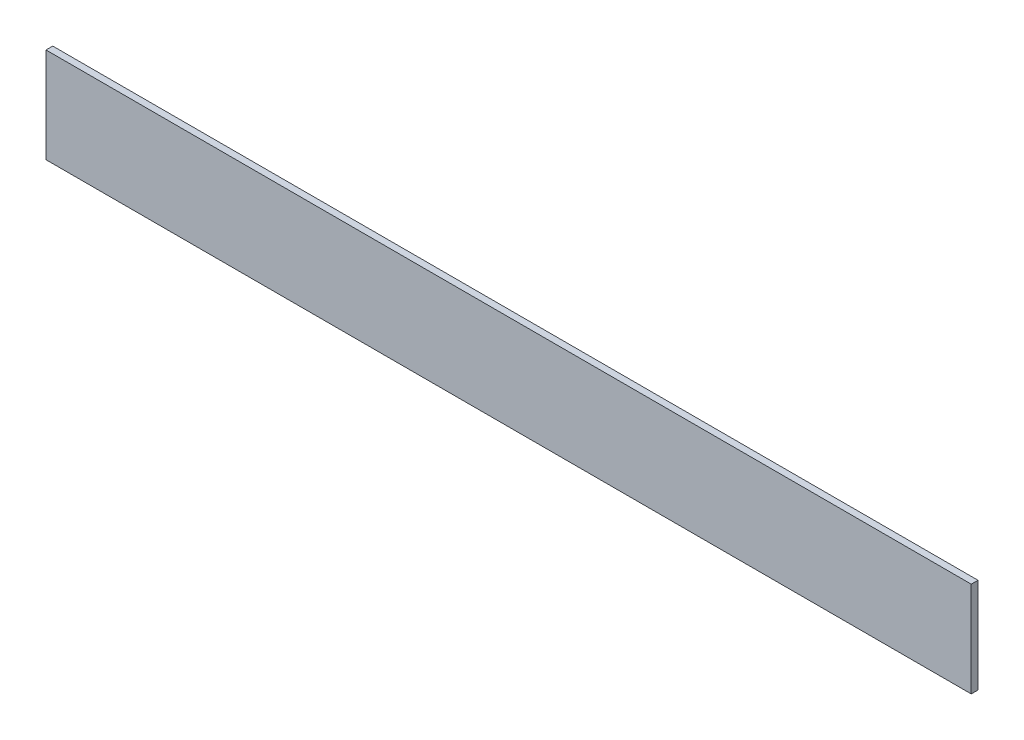
SolidWorks part; units mm, degrees
ref_plane "Front Plane" through (0, 0, 0) normal (0, 0, 1) x (1, 0, 0)
ref_plane "Top Plane" through (0, 0, 0) normal (0, 1, 0) x (1, 0, 0)
ref_plane "Right Plane" through (0, 0, 0) normal (1, 0, 0) x (0, 0, -1)
sketch "Sketch1" plane through (0, 0, 0) normal (0, 0, 1) x (1, 0, 0)
  line L1 (-217.4875, -22.352) -> (217.4875, -22.352)
  line L2 (-217.4875, -22.352) -> (-217.4875, 22.352)
  line L3 (-217.4875, 22.352) -> (217.4875, 22.352)
  line L4 (217.4875, -22.352) -> (217.4875, 22.352)
  line L5 (-217.4875, -22.352) -> (217.4875, 22.352) construction
  line L6 (-217.4875, 22.352) -> (217.4875, -22.352) construction
  point P0 (0, 0)
  dimension "D1" = 44.704
  dimension "D2" = 434.975
extrude "Boss-Extrude1" add sketch "Sketch1" along normal blind 3.175
sketch "Sketch5" plane through (0, 0, 3.175) normal (0, 0, 1) x (1, 0, 0)
  line L8 (217.4875, 38.608) -> (217.4875, 68.072)
  line L9 (-204.7875, 25.908) -> (204.7875, 25.908)
  line L10 (-217.4875, 68.072) -> (-217.4875, 38.608)
  line L11 (214.9475, 70.612) -> (-214.9475, 70.612)
  line L12 (217.4875, 86.868) -> (217.4875, 116.332)
  line L13 (-204.7875, 74.168) -> (204.7875, 74.168)
  line L14 (-217.4875, 116.332) -> (-217.4875, 86.868)
  line L15 (214.9475, 118.872) -> (-214.9475, 118.872)
  line L16 (217.4875, 135.128) -> (217.4875, 164.592)
  line L17 (-204.7875, 122.428) -> (204.7875, 122.428)
  line L18 (-217.4875, 164.592) -> (-217.4875, 135.128)
  line L19 (214.9475, 167.132) -> (-214.9475, 167.132)
  line L20 (217.4875, 183.388) -> (217.4875, 212.852)
  line L21 (-204.7875, 170.688) -> (204.7875, 170.688)
  line L22 (-217.4875, 212.852) -> (-217.4875, 183.388)
  line L23 (214.9475, 215.392) -> (-214.9475, 215.392)
  line L24 (217.4875, 231.648) -> (217.4875, 261.112)
  line L25 (-204.7875, 218.948) -> (204.7875, 218.948)
  line L26 (-217.4875, 261.112) -> (-217.4875, 231.648)
  line L27 (214.9475, 263.652) -> (-214.9475, 263.652)
  line L28 (217.4875, 279.908) -> (217.4875, 309.372)
  line L29 (-204.7875, 267.208) -> (204.7875, 267.208)
  line L30 (-217.4875, 309.372) -> (-217.4875, 279.908)
  line L31 (214.9475, 311.912) -> (-214.9475, 311.912)
  circle A12 centre (166.6875, 60.96) radius 2.8956
  arc A13 (217.4875, 68.072) -> (214.9475, 70.612) centre (214.9475, 68.072) ccw
  arc A14 (204.7875, 25.908) -> (217.4875, 38.608) centre (204.7875, 38.608) ccw
  circle A15 centre (-166.6875, 60.96) radius 2.8956
  arc A16 (-217.4875, 38.608) -> (-204.7875, 25.908) centre (-204.7875, 38.608) ccw
  arc A17 (-214.9475, 70.612) -> (-217.4875, 68.072) centre (-214.9475, 68.072) ccw
  circle A18 centre (166.6875, 109.22) radius 2.8956
  arc A19 (217.4875, 116.332) -> (214.9475, 118.872) centre (214.9475, 116.332) ccw
  arc A20 (204.7875, 74.168) -> (217.4875, 86.868) centre (204.7875, 86.868) ccw
  circle A21 centre (-166.6875, 109.22) radius 2.8956
  arc A22 (-217.4875, 86.868) -> (-204.7875, 74.168) centre (-204.7875, 86.868) ccw
  arc A23 (-214.9475, 118.872) -> (-217.4875, 116.332) centre (-214.9475, 116.332) ccw
  circle A24 centre (166.6875, 157.48) radius 2.8956
  arc A25 (217.4875, 164.592) -> (214.9475, 167.132) centre (214.9475, 164.592) ccw
  arc A26 (204.7875, 122.428) -> (217.4875, 135.128) centre (204.7875, 135.128) ccw
  circle A27 centre (-166.6875, 157.48) radius 2.8956
  arc A28 (-217.4875, 135.128) -> (-204.7875, 122.428) centre (-204.7875, 135.128) ccw
  arc A29 (-214.9475, 167.132) -> (-217.4875, 164.592) centre (-214.9475, 164.592) ccw
  circle A30 centre (166.6875, 205.74) radius 2.8956
  arc A31 (217.4875, 212.852) -> (214.9475, 215.392) centre (214.9475, 212.852) ccw
  arc A32 (204.7875, 170.688) -> (217.4875, 183.388) centre (204.7875, 183.388) ccw
  circle A33 centre (-166.6875, 205.74) radius 2.8956
  arc A34 (-217.4875, 183.388) -> (-204.7875, 170.688) centre (-204.7875, 183.388) ccw
  arc A35 (-214.9475, 215.392) -> (-217.4875, 212.852) centre (-214.9475, 212.852) ccw
  circle A36 centre (166.6875, 254) radius 2.8956
  arc A37 (217.4875, 261.112) -> (214.9475, 263.652) centre (214.9475, 261.112) ccw
  arc A38 (204.7875, 218.948) -> (217.4875, 231.648) centre (204.7875, 231.648) ccw
  circle A39 centre (-166.6875, 254) radius 2.8956
  arc A40 (-217.4875, 231.648) -> (-204.7875, 218.948) centre (-204.7875, 231.648) ccw
  arc A41 (-214.9475, 263.652) -> (-217.4875, 261.112) centre (-214.9475, 261.112) ccw
  circle A42 centre (166.6875, 302.26) radius 2.8956
  arc A43 (217.4875, 309.372) -> (214.9475, 311.912) centre (214.9475, 309.372) ccw
  arc A44 (204.7875, 267.208) -> (217.4875, 279.908) centre (204.7875, 279.908) ccw
  circle A45 centre (-166.6875, 302.26) radius 2.8956
  arc A46 (-217.4875, 279.908) -> (-204.7875, 267.208) centre (-204.7875, 279.908) ccw
  arc A47 (-214.9475, 311.912) -> (-217.4875, 309.372) centre (-214.9475, 309.372) ccw
extrude "Boss-Extrude4" [suppressed] add sketch "Sketch5" along normal blind 2.54 separate body
